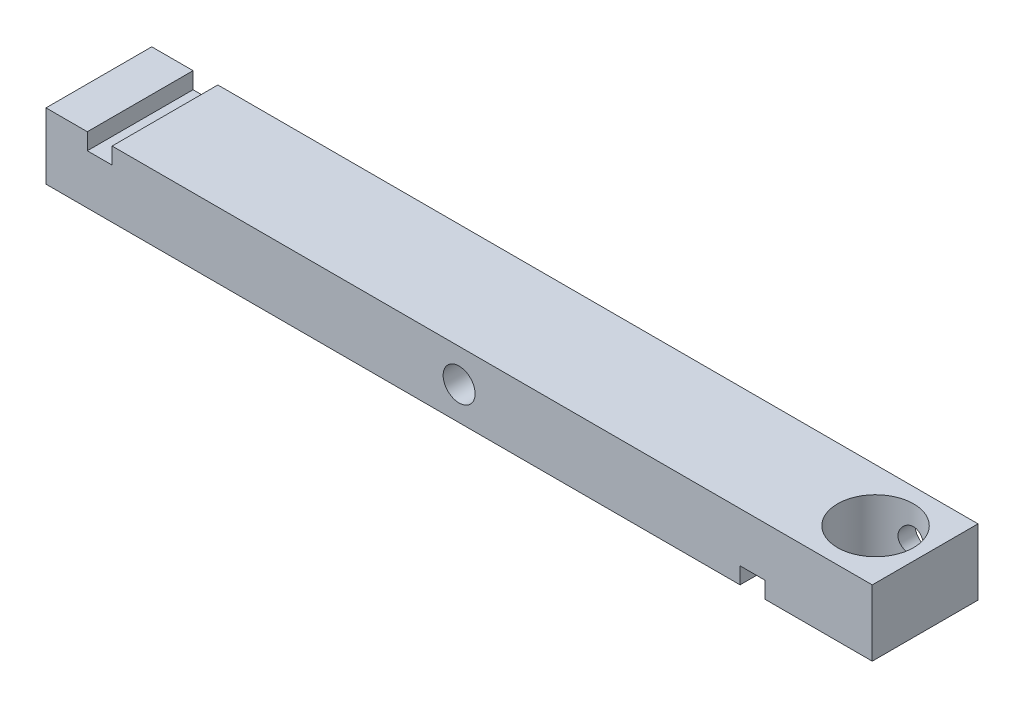
SolidWorks part; units mm, degrees
ref_plane "Front Plane" through (0, 0, 0) normal (0, 0, 1) x (1, 0, 0)
ref_plane "Top Plane" through (0, 0, 0) normal (0, 1, 0) x (1, 0, 0)
ref_plane "Right Plane" through (0, 0, 0) normal (1, 0, 0) x (0, 0, -1)
sketch "Sketch1" plane through (0, 0, 0) normal (0, 0, 1) x (1, 0, 0)
  line L1 (-63.5, -5.08) -> (63.5, -5.08)
  line L2 (-63.5, -5.08) -> (-63.5, 5.08)
  line L3 (-63.5, 5.08) -> (63.5, 5.08)
  line L4 (63.5, -5.08) -> (63.5, 5.08)
  line L5 (-63.5, -5.08) -> (63.5, 5.08) construction
  line L6 (-63.5, 5.08) -> (63.5, -5.08) construction
  point P0 (0, 0)
  dimension "D1" = 10.16
  dimension "D2" = 127
extrude "Boss-Extrude1" add sketch "Sketch1" along normal mid plane 16.256
hole_wizard "#10 (0.1935) Diameter Hole2" positions "Sketch4" profile "Sketch5" hole size "#10" standard "ANSI Inch" end condition through all
sketch "Sketch4" plane through (0, 0, 8.128) normal (0, 0, 1) x (1, 0, 0)
  point P0 (0, 0)
sketch "Sketch5" plane through (0, 0, 8.128) normal (1, 0, 0) x (0, -1, 0)
  line L0 (0, 0) -> (0, 16.256)
  line L1 (0, 16.256) -> (2.4574, 16.256)
  line L2 (2.4574, 16.256) -> (2.4574, 0)
  line L5 (2.4574, 0) -> (0, 0)
  line L11 (0, -6.35) -> (0, 107.95) construction
  dimension "Thru Hole Dia." = 4.9149
  dimension "Thru Hole Depth" = 16.256
sketch "Sketch6" plane through (0, 0, 8.128) normal (0, 0, 1) x (1, 0, 0)
  line L0 (-57.15, 5.08) -> (-57.15, 2.54)
  line L1 (43.18, -2.54) -> (43.18, -5.08)
  line L2 (-57.15, 2.54) -> (-53.34, 2.54)
  line L3 (-53.34, 2.54) -> (-53.34, 5.08)
  line L4 (-57.15, 5.08) -> (-53.34, 5.08)
  line L5 (63.5, 5.08) -> (-63.5, 5.08) construction
  line L6 (43.18, -5.08) -> (46.99, -5.08)
  line L7 (46.99, -5.08) -> (46.99, -2.54)
  line L8 (43.18, -2.54) -> (46.99, -2.54)
  line L9 (-63.5, -5.08) -> (63.5, -5.08) construction
  dimension "D4" = 2.54
  dimension "D1" = 53.34
  dimension "D2" = 2.54
  dimension "D3" = 57.15
  dimension "D5" = 43.18
  dimension "D6" = 3.81
extrude "Cut-Extrude1" cut sketch "Sketch6" against normal up to surface (16.256 mm away) up to face at (2.4574, 0, -8.128)
hole_wizard "Hole1" positions "Sketch7" profile "Sketch8" legacy end condition through all
sketch "Sketch7" plane through (0, 5.08, 0) normal (0, 1, 0) x (1, 0, 0)
  point P0 (55.88, 0)
  dimension "D1" = 55.88
sketch "Sketch8" plane through (55.88, 5.08, 0) normal (1, 0, 0) x (0, 0, 1)
  line L0 (0, 0) -> (0, 10.16)
  line L1 (0, 10.16) -> (5.842, 10.16)
  line L2 (5.842, 10.16) -> (5.842, 0)
  line L3 (5.842, 0) -> (0, 0)
  line L4 (0, 110) -> (0, -10) construction
  dimension "Diameter" = 11.684
  dimension "Depth" = 10.16
hole_wizard "Hole2" positions "Sketch9" profile "Sketch11" legacy
sketch "Sketch9" plane through (0, 0, -8.128) normal (0, 0, -1) x (-1, 0, 0)
  point P0 (-55.88, 0)
  dimension "D1" = 55.88
sketch "Sketch11" plane through (55.88, 0, -8.128) normal (1, 0, 0) x (0, 1, 0)
  line L0 (0, 0) -> (0, 8.127)
  line L1 (0, 8.127) -> (2.032, 6.9061)
  line L2 (2.032, 6.9061) -> (2.032, 0)
  line L5 (2.032, 0) -> (0, 0)
  line L10 (0, 8.127) -> (-2.032, 6.9061) construction
  line L11 (0, -6.35) -> (0, 107.95) construction
  dimension "Hole Dia." = 4.064
  dimension "Hole Depth" = 8.127
  dimension "Drill Angle" = 118
